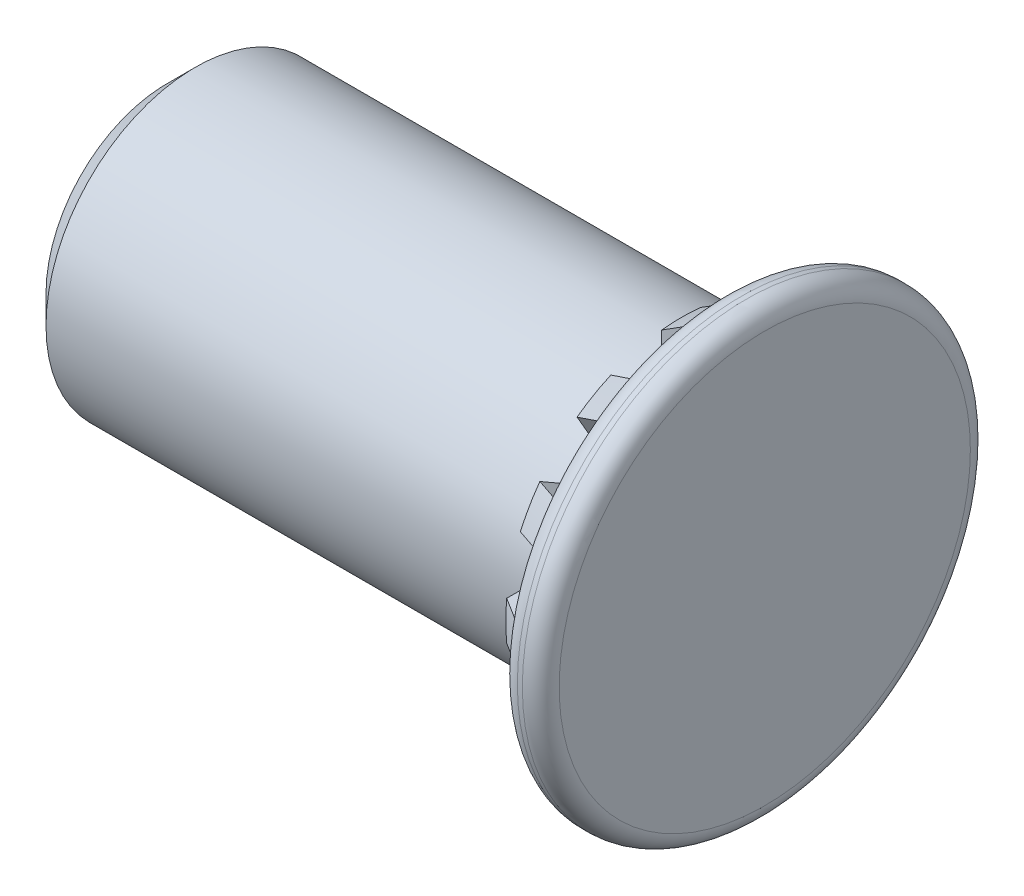
SolidWorks part; units mm, degrees
material "AISI 304"
ref_plane "Front Plane" through (0, 0, 0) normal (0, 0, 1) x (1, 0, 0)
ref_plane "Top Plane" through (0, 0, 0) normal (0, 1, 0) x (1, 0, 0)
ref_plane "Right Plane" through (0, 0, 0) normal (1, 0, 0) x (0, 0, -1)
sketch "Sketch1" plane through (0, 0, 0) normal (0, 0, 1) x (1, 0, 0)
  line L0 (99.3396, 0) -> (-101.9247, 0) construction
  line L1 (2.475, 0) -> (-2.475, 0) construction
  line L2 (0, 0) -> (0, 2.25)
  line L3 (0, -2.475) -> (0, 2.475) construction
  line L4 (0, 2.25) -> (-0.42, 2.25)
  line L5 (-0.42, 2.25) -> (-0.42, 1.763)
  line L6 (-0.42, 1.763) -> (-0.578, 1.763)
  line L7 (-0.578, 1.763) -> (-0.578, 1.5)
  line L8 (-0.578, 1.5) -> (-6, 1.5)
  line L9 (-6, 1.5) -> (-6, 0)
  line L10 (-6, 0) -> (0, 0)
  dimension "D1" = 4.5
  dimension "D2" = 3
  dimension "D3" = 6
  dimension "D4" = 0.42
  dimension "D5" = 0.158
  dimension "D6" = 3.526
revolve "Revolve1" add sketch "Sketch1" angle 360 about L0
chamfer "Chamfer1" distance 0.281 angle 45 1 edges at (-6, 0, -1.5)
fillet "Fillet1" radius 0.185 2 edges at (0, 0, -2.25) (-0.42, 0, -2.25)
sketch "Sketch2" plane through (-0.42, 0, 0) normal (-1, 0, 0) x (0, 0, 1)
  line L0 (0.196, 2.0155) -> (0.196, 1.4871)
  line L1 (0, 2.7995) -> (0, 1.2502) construction
  line L2 (-0.196, 2.0155) -> (-0.196, 1.4871)
  arc A0 (0.196, 2.0155) -> (-0.196, 2.0155) centre (0, 0) ccw
  circle A1 centre (0, 0) radius 1.5 construction
  circle A2 centre (0, 0) radius 1.5
  circle M5 centre (0, 0) radius 1.763
  dimension "D2" = 2.025
  dimension "D1" = 0.392
extrude "Boss-Extrude1" add sketch "Sketch2" along normal blind 0.42 contours A0 L1 L0 M5 | L1 A2 L0 M5 | L1 A0 L2 M5 | L1 L2 A2 M5
sketch "Sketch3" plane through (0, 0, 0) normal (0, 0, 1) x (1, 0, 0)
  line L0 (-0.42, 2.025) -> (-0.84, 1.762)
  line L1 (-0.84, 1.762) -> (-0.84, 2.025)
  line L2 (-0.84, 2.025) -> (-0.42, 2.025)
  line L3 (-0.84, 2.0155) -> (-0.84, 1.4871) construction
  line L4 (-0.42, 2.025) -> (-0.42, 2.0155) construction
  line L5 (-6.6252, 0) -> (1.0631, -0.0661) construction
  dimension "D1" = 0.263
revolve "Cut-Revolve1" cut sketch "Sketch3" angle 360 about L5
pattern_circular "CirPattern1" count 12 over 360 about axis through (0, 0, 0) along (1, 0, 0) of "Cut-Revolve1", "Boss-Extrude1"
